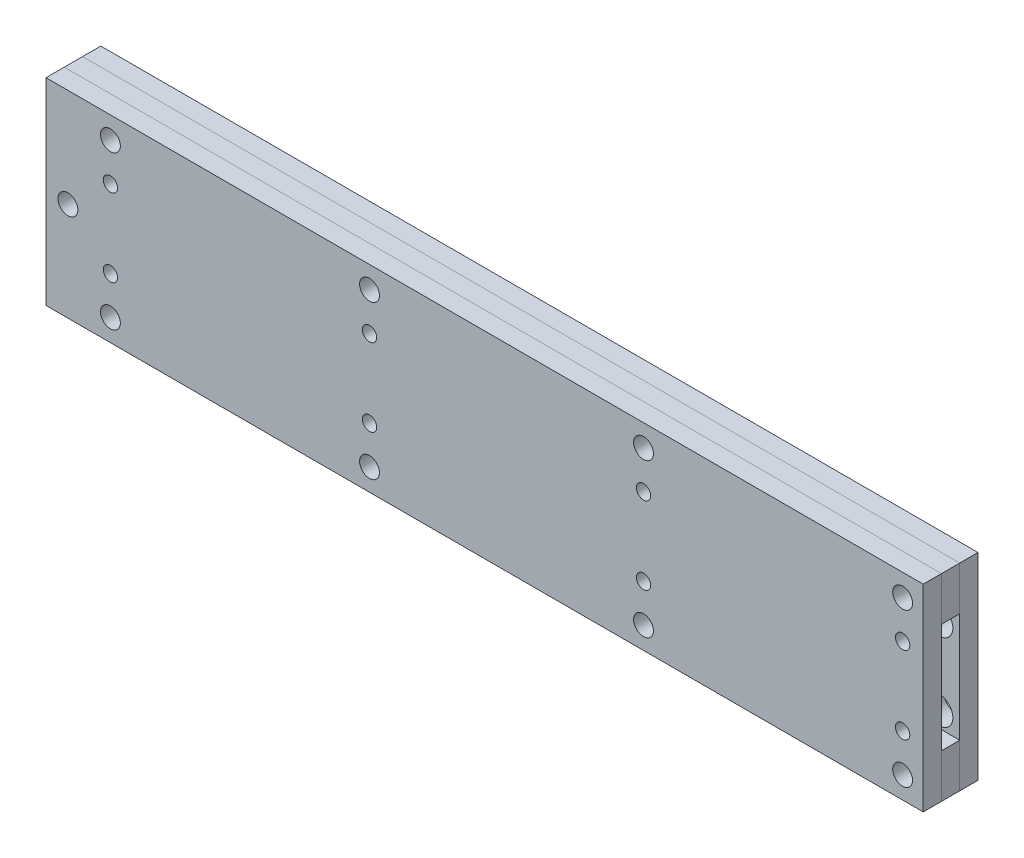
SolidWorks part; units mm, degrees
ref_plane "Alzado" through (0, 0, 0) normal (0, 0, 1) x (1, 0, 0)
ref_plane "Planta" through (0, 0, 0) normal (0, 1, 0) x (1, 0, 0)
ref_plane "Vista lateral" through (0, 0, 0) normal (1, 0, 0) x (0, 0, -1)
sketch "Croquis1" plane through (0, 0, 0) normal (0, 0, 1) x (1, 0, 0)
  line L0 (-144.8435, 13.4874) -> (144.8435, 13.4874) construction
  line L1 (-144.8435, -19.05) -> (144.8435, -19.05)
  line L2 (-144.8435, -19.05) -> (-144.8435, 19.05)
  line L3 (-144.8435, 19.05) -> (144.8435, 19.05)
  line L4 (144.8435, -19.05) -> (144.8435, 19.05)
  line L5 (-144.8435, -19.05) -> (144.8435, 19.05) construction
  line L6 (-144.8435, 19.05) -> (144.8435, -19.05) construction
  line L7 (0, 19.05) -> (0, -19.05) construction
  circle A0 centre (-137.6934, 13.4874) radius 4.7561
  circle A1 centre (-47.625, 13.4874) radius 4.7562
  circle A2 centre (137.6934, 13.4874) radius 4.7561
  circle A3 centre (47.625, 13.4874) radius 4.7562
  circle A4 centre (137.6934, -13.5128) radius 4.7561
  circle A5 centre (47.625, -13.5128) radius 4.7562
  circle A6 centre (-47.625, -13.5128) radius 4.7562
  circle A7 centre (-137.6934, -13.5128) radius 4.7561
  point P0 (0, 0)
  dimension "D5" = 9.5123
  dimension "D1" = 289.687
  dimension "D2" = 38.1
  dimension "D3" = 5.5626
  dimension "D4" = 95.25
  dimension "D6" = 90.0684
  dimension "D7" = 27.0002
sketch "Croquis3" plane through (0, 0, 0) normal (0, 0, 1) x (1, 0, 0)
  line L0 (-144.8435, 19.05) -> (144.8435, 19.05) construction
  line L1 (-160.0835, -34.29) -> (160.0835, -34.29)
  line L2 (-160.0835, -34.29) -> (-160.0835, 34.29)
  line L3 (-160.0835, 34.29) -> (160.0835, 34.29)
  line L4 (160.0835, -34.29) -> (160.0835, 34.29)
  line L5 (-160.0835, -34.29) -> (160.0835, 34.29) construction
  line L6 (-160.0835, 34.29) -> (160.0835, -34.29) construction
  line L7 (-144.8435, -19.05) -> (-144.8435, 19.05) construction
  line L8 (-152.4635, -34.29) -> (-152.4635, 34.29) construction
  line L9 (-160.0835, 26.67) -> (160.0835, 26.67) construction
  line L10 (-144.8435, 0) -> (-160.0835, 0) construction
  line L11 (144.8435, 34.29) -> (144.8435, -34.29)
  line L12 (144.8435, -19.05) -> (144.8435, 19.05) construction
  circle A0 centre (-152.4635, 0) radius 2.4892
  circle A1 centre (-137.6934, 26.67) radius 2.4892
  circle A2 centre (-47.625, 26.67) radius 2.4892
  circle A3 centre (47.625, 26.67) radius 2.4892
  circle A4 centre (137.6934, 26.67) radius 2.4892
  circle A5 centre (137.6934, 13.4874) radius 4.7561 construction
  circle A6 centre (47.625, 13.4874) radius 4.7562 construction
  circle A7 centre (-47.625, 13.4874) radius 4.7562 construction
  circle A8 centre (-137.6934, 13.4874) radius 4.7561 construction
  circle A9 centre (137.6934, 13.4874) radius 4.7561
  circle A10 centre (47.625, 13.4874) radius 4.7562
  circle A11 centre (-47.625, 13.4874) radius 4.7562
  circle A12 centre (-137.6934, 13.4874) radius 4.7561
  circle A13 centre (-137.6934, -13.4874) radius 4.7561
  circle A14 centre (-47.625, -13.4874) radius 4.7562
  circle A15 centre (47.625, -13.4874) radius 4.7562
  circle A16 centre (137.6934, -13.4874) radius 4.7561
  circle A17 centre (137.6934, -26.67) radius 2.4892
  circle A18 centre (47.625, -26.67) radius 2.4892
  circle A19 centre (-47.625, -26.67) radius 2.4892
  circle A20 centre (-137.6934, -26.67) radius 2.4892
  point P0 (0, 0)
  dimension "D5" = 4.9784
  dimension "D1" = 15.24
  dimension "D2" = 15.24
  dimension "D3" = 7.62
  dimension "D4" = 7.62
extrude "Saliente-Extruir1" add sketch "Croquis3" along normal blind 6.35 contours L11 L3 L2 L1 A19 A17 A15 A13 A12 A11 A10 A9 A4 A3 A2 A1 A0 A14 A16 A18 A20
sketch "Croquis4" plane through (0, 0, 6.35) normal (0, 0, 1) x (1, 0, 0)
  line L0 (-144.8435, 19.05) -> (144.8435, 19.05) construction
  line L1 (-144.8435, -19.05) -> (-144.8435, 19.05) construction
  line L2 (-144.8435, -19.05) -> (144.8435, -19.05) construction
  line L3 (-144.8435, -19.05) -> (144.8435, -19.05)
  line L4 (144.8435, -34.29) -> (144.8435, 34.29)
  line L5 (144.8435, 34.29) -> (-160.0835, 34.29)
  line L6 (-160.0835, 34.29) -> (-160.0835, -34.29)
  line L7 (-160.0835, -34.29) -> (144.8435, -34.29)
  line L8 (144.8435, -34.29) -> (144.8435, 34.29)
  line L9 (144.8435, 34.29) -> (-160.0835, 34.29)
  line L10 (-160.0835, 34.29) -> (-160.0835, -34.29)
  line L11 (-160.0835, -34.29) -> (144.8435, -34.29)
  line L12 (-144.8435, -19.05) -> (-144.8435, 19.05)
  line L13 (-144.8435, 19.05) -> (144.8435, 19.05)
  line L14 (-144.8435, 0) -> (-152.4635, 0) construction
  circle A0 centre (-137.6934, 26.67) radius 2.4892
  circle A1 centre (-152.4635, 0) radius 2.4892
  circle A2 centre (-47.625, 26.67) radius 2.4892
  circle A3 centre (47.625, 26.67) radius 2.4892
  circle A4 centre (137.6934, 26.67) radius 2.4892
  circle A5 centre (137.6934, -26.67) radius 2.4892
  circle A6 centre (47.625, -26.67) radius 2.4892
  circle A7 centre (-47.625, -26.67) radius 2.4892
  circle A8 centre (-137.6934, -26.67) radius 2.4892
  dimension "D2" = 4.9784
  dimension "D1" = 0
extrude "Saliente-Extruir2" add sketch "Croquis4" along normal blind 6.35 separate body
sketch "Croquis7" plane through (0, 0, 12.7) normal (0, 0, 1) x (1, 0, 0)
  line L0 (-144.8435, -19.05) -> (144.8435, -19.05) construction
  line L1 (-144.8435, -19.05) -> (-144.8435, 19.05) construction
  line L2 (-144.8435, 19.05) -> (144.8435, 19.05) construction
  line L3 (-144.8435, -19.05) -> (144.8435, -19.05)
  line L4 (144.8435, -34.29) -> (144.8435, 34.29)
  line L5 (144.8435, 34.29) -> (-160.0835, 34.29)
  line L6 (-160.0835, 34.29) -> (-160.0835, -34.29)
  line L7 (-160.0835, -34.29) -> (144.8435, -34.29)
  line L8 (144.8435, -34.29) -> (144.8435, 34.29)
  line L9 (144.8435, 34.29) -> (-160.0835, 34.29)
  line L10 (-160.0835, 34.29) -> (-160.0835, -34.29)
  line L11 (-160.0835, -34.29) -> (144.8435, -34.29)
  line L12 (-144.8435, -19.05) -> (-144.8435, 19.05)
  line L13 (-144.8435, 19.05) -> (144.8435, 19.05)
  line L14 (-144.8435, 0) -> (144.8435, 0) construction
  circle A0 centre (-137.6934, 13.4874) radius 2.4892
  circle A1 centre (-152.4635, 0) radius 3.45
  circle A3 centre (-137.6934, 26.67) radius 3.45
  circle A5 centre (-47.625, 26.67) radius 3.45
  circle A7 centre (47.625, 26.67) radius 3.45
  circle A9 centre (137.6934, 26.67) radius 3.45
  circle A11 centre (137.6934, -26.67) radius 3.45
  circle A13 centre (47.625, -26.67) radius 3.45
  circle A15 centre (-47.625, -26.67) radius 3.45
  circle A17 centre (-137.6934, -26.67) radius 3.45
  circle A19 centre (-137.6934, -13.4874) radius 2.4892
  circle A20 centre (-47.625, 13.4874) radius 2.4892
  circle A21 centre (-47.625, -13.4874) radius 2.4892
  circle A22 centre (47.625, -13.4874) radius 2.4892
  circle A23 centre (47.625, 13.4874) radius 2.4892
  circle A24 centre (137.6934, 13.4874) radius 2.4892
  circle A25 centre (137.6934, -13.4874) radius 2.4892
  line M14 (-144.8435, -19.05) -> (-144.8435, 19.05)
  line M15 (-144.8435, 19.05) -> (144.8435, 19.05)
  line M16 (144.8435, 19.05) -> (144.8435, 34.29)
  line M17 (144.8435, 34.29) -> (-160.0835, 34.29)
  line M18 (-160.0835, 34.29) -> (-160.0835, -34.29)
  line M19 (-160.0835, -34.29) -> (144.8435, -34.29)
  line M20 (144.8435, -34.29) -> (144.8435, -19.05)
  line M21 (144.8435, -19.05) -> (-144.8435, -19.05)
  circle M22 centre (-152.4635, 0) radius 2.4892
  circle M23 centre (137.6934, -26.67) radius 2.4892
  circle M24 centre (47.625, 26.67) radius 2.4892
  circle M25 centre (-137.6934, 26.67) radius 2.4892
  circle M26 centre (-137.6934, -26.67) radius 2.4892
  circle M27 centre (47.625, -26.67) radius 2.4892
  circle M28 centre (-47.625, 26.67) radius 2.4892
  circle M29 centre (137.6934, 26.67) radius 2.4892
  circle M30 centre (-47.625, -26.67) radius 2.4892
  dimension "D1" = 4.9784
  dimension "D2" = 6.9
  dimension "D4" = 0
extrude "Saliente-Extruir4" add sketch "Croquis7" along normal blind 6.35 separate body contours M21 M14 M15 M16 M17 M18 M19 M20 M22 M24 M26 M28 M30 M29 M27 M25 M23 | L8 A25 A24 A23 A22 A21 A20 A19 A0 M21 M15 M14 | L12 L14 L8 A0 A20 A23 A24 M15
equation "\"hole\"= 0.3745"
equation "\"D5@Croquis1\"=\"hole\""
equation "\"D3@Croquis3\"=\"D2@Croquis3\"/2"
equation "\"D4@Croquis3\"=\"D1@Croquis3\"/2"
